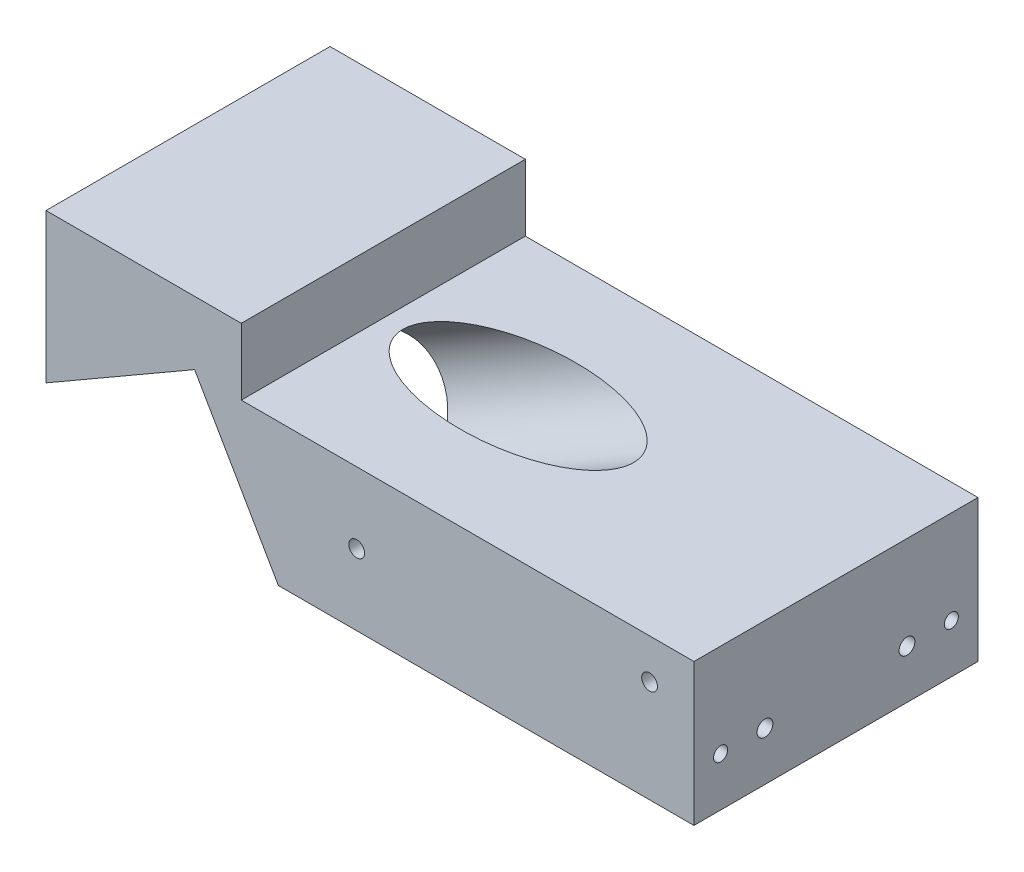
SolidWorks part; units mm, degrees
material "6061-T4 (SS)"
ref_plane "Front Plane" through (0, 0, 0) normal (0, 0, 1) x (1, 0, 0)
ref_plane "Top Plane" through (0, 0, 0) normal (0, 1, 0) x (1, 0, 0)
ref_plane "Right Plane" through (0, 0, 0) normal (1, 0, 0) x (0, 0, -1)
sketch "Sketch1" plane through (0, 0, 0) normal (0, 1, 0) x (1, 0, 0)
  line L1 (-36.5, 16) -> (36.5, 16)
  line L2 (-36.5, 16) -> (-36.5, -16)
  line L3 (-36.5, -16) -> (36.5, -16)
  line L4 (36.5, 16) -> (36.5, -16)
  line L5 (-36.5, 16) -> (36.5, -16) construction
  line L6 (-36.5, -16) -> (36.5, 16) construction
  point P0 (0, 0)
  dimension "D1" = 73
  dimension "D2" = 32
extrude "Boss-Extrude1" add sketch "Sketch1" along normal blind 16
sketch "Sketch78" plane through (0, 0, 16) normal (0, 0, 1) x (1, 0, 0)
  line L1 (-36.5, 16) -> (-14.5, 16)
  line L2 (-36.5, 16) -> (-36.5, 23.5)
  line L3 (-36.5, 23.5) -> (-14.5, 23.5)
  line L4 (-14.5, 16) -> (-14.5, 23.5)
  dimension "D1" = 7.5
  dimension "D2" = 22
extrude "Boss-Extrude4" add sketch "Sketch78" against normal up to surface (32 mm away) up to face at (0, 8, -16)
sketch "Sketch79" plane through (0, 0, -16) normal (0, 0, -1) x (-1, 0, 0)
  line L0 (-32.5, 1.97) -> (23.61, 1.97) construction
  line L1 (-32.5, 1.97) -> (-32.5, 29.2) construction
  line L2 (23.61, 1.97) -> (-20.8992, 27.6674) construction
  line L3 (33.135, 1.97) -> (34.135, 1.97) construction
  line L4 (14.4951, 7.2325) -> (19.7576, 16.3474)
  line L5 (19.7576, 16.3474) -> (36.5, 6.6812)
  line L6 (36.5, 23.5) -> (36.5, 0) construction
  line L7 (14.4951, 7.2325) -> (10.3194, 0)
  line L8 (-36.5, 0) -> (36.5, 0) construction
  line L9 (10.3194, 0) -> (36.5, 0)
  line L10 (36.5, 0) -> (36.5, 6.6812)
  circle A0 centre (23.61, 1.97) radius 9.525 construction
  circle A1 centre (23.61, 1.97) radius 10.525 construction
  dimension "D4" = 19.05
  dimension "D1" = 27.23
  dimension "D2" = 56.11
  dimension "D3" = 30
  dimension "D5" = 1
extrude "Cut-Extrude23" cut sketch "Sketch79" against normal blind 41
sketch "Sketch26" plane through (0, 0, 0) normal (0, -1, 0) x (1, 0, 0)
  line L0 (-10.3194, 16) -> (36.5, 16) construction
  line L1 (36.5, -16) -> (42.85, -16)
  line L2 (36.5, -16) -> (36.5, 16)
  line L3 (36.5, 16) -> (42.85, 16)
  line L4 (42.85, -16) -> (42.85, 16)
  dimension "D1" = 6.35
sketch "Sketch15" plane through (-36.5, 0, 0) normal (-1, 0, 0) x (0, 0, 1)
  line L0 (-10, 14.6812) -> (10, 14.6812) construction
  line L1 (-10, 14.6812) -> (-16, 14.6812) construction
  line L3 (10, 14.6812) -> (16, 14.6812) construction
  line L6 (16, 23.5) -> (16, 6.6812) construction
  line L7 (-16, 23.5) -> (-16, 6.6812) construction
  line L9 (16, 6.6812) -> (-16, 6.6812) construction
  dimension "D3" = 20
  dimension "D4" = 8
sketch "Sketch14" plane through (-13.4261, 5.3809, -20) normal (-0.866, -0.5, 0) x (0, 0, 1)
  line L0 (4, 2.138) -> (20, 2.138) construction
  line L1 (20, 2.138) -> (36, 2.138) construction
  line L2 (36, 12.663) -> (36, -6.2133) construction
  line L3 (4, 12.663) -> (4, -6.2133) construction
  circle A0 centre (20, 2.138) radius 6.5
  dimension "D1" = 13
extrude "Cut-Extrude2" cut sketch "Sketch14" against normal blind 33 and the other way blind 41
hole_wizard "#2-56 Tapped Hole1" positions "Sketch80" profile "Sketch81" tap size "#2-56" standard "ANSI Inch"
sketch "Sketch80" plane through (-36.5, 0, 0) normal (-1, 0, 0) x (0, 0, 1)
  point P0 (-10, 14.6812)
  point P3 (10, 14.6812)
sketch "Sketch81" plane through (-36.5, 14.6812, -10) normal (0, 1, 0) x (0, 0, 1)
  line L0 (0, 0) -> (0, 6.8842)
  line L1 (0, 6.8842) -> (0.889, 6.35)
  line L2 (0.889, 6.35) -> (0.889, 0)
  line L5 (0.889, 0) -> (0, 0)
  line L10 (0, 6.8842) -> (-0.889, 6.35) construction
  line L11 (0, -6.35) -> (0, 107.95) construction
  dimension "Tap Drill Dia." = 1.778
  dimension "Tap Drill Depth" = 6.35
  dimension "Drill Angle" = 118
cosmetic thread "Hole Thread1" parameters "D1"=4.4, "D2"=2.1844
cosmetic thread "Hole Thread2" parameters "D1"=4.4, "D2"=2.1844
sketch "Sketch59" plane through (0, 0, -16) normal (0, 0, -1) x (-1, 0, 0)
  line L0 (36.5, 16) -> (36.5, 0) construction
  line L1 (36.5, 0) -> (-36.5, 0) construction
  line L2 (-36.5, 0) -> (-36.5, 16) construction
  line L3 (36.5, 23.5) -> (36.5, 6.6812) construction
  line L4 (-36.5, 16) -> (36.5, 16) construction
  line L5 (-36.5, 8) -> (36.5, 8) construction
  line L7 (-36.5, 16) -> (14.5, 16) construction
  line L8 (-31.5, 11.5) -> (-31.5, 8) construction
  line L10 (-36.5, 16) -> (-36.5, 0) construction
  point P10 (-31.5, 11.5)
  point P11 (1.5, 8)
  dimension "D1" = 5
  dimension "D2" = 35
  dimension "D3" = 3.5
hole_wizard "#2-56 Tapped Hole2" positions "Sketch82" profile "Sketch83" tap size "#2-56" standard "ANSI Inch"
sketch "Sketch82" plane through (0, 0, -16) normal (0, 0, -1) x (-1, 0, 0)
  point P0 (-31.5, 11.5)
  point P3 (1.5, 8)
sketch "Sketch83" plane through (31.5, 11.5, -16) normal (1, 0, 0) x (0, 1, 0)
  line L0 (0, 0) -> (0, 6.8842)
  line L1 (0, 6.8842) -> (0.889, 6.35)
  line L2 (0.889, 6.35) -> (0.889, 0)
  line L5 (0.889, 0) -> (0, 0)
  line L10 (0, 6.8842) -> (-0.889, 6.35) construction
  line L11 (0, -6.35) -> (0, 107.95) construction
  dimension "Tap Drill Dia." = 1.778
  dimension "Tap Drill Depth" = 6.35
  dimension "Drill Angle" = 118
cosmetic thread "Hole Thread3" parameters "D1"=4.4, "D2"=2.1844
cosmetic thread "Hole Thread4" parameters "D1"=4.4, "D2"=2.1844
hole_wizard "#2-56 Tapped Hole3" positions "Sketch84" profile "Sketch85" tap size "#2-56" standard "ANSI Inch"
sketch "Sketch84" plane through (0, 0, 16) normal (0, 0, 1) x (1, 0, 0)
  point P0 (-1.5, 8)
  point P3 (31.5, 11.5)
sketch "Sketch85" plane through (-1.5, 8, 16) normal (1, 0, 0) x (0, -1, 0)
  line L0 (0, 0) -> (0, 6.8842)
  line L1 (0, 6.8842) -> (0.889, 6.35)
  line L2 (0.889, 6.35) -> (0.889, 0)
  line L5 (0.889, 0) -> (0, 0)
  line L10 (0, 6.8842) -> (-0.889, 6.35) construction
  line L11 (0, -6.35) -> (0, 107.95) construction
  dimension "Tap Drill Dia." = 1.778
  dimension "Tap Drill Depth" = 6.35
  dimension "Drill Angle" = 118
cosmetic thread "Hole Thread5" parameters "D1"=4.4, "D2"=2.1844
cosmetic thread "Hole Thread6" parameters "D1"=4.4, "D2"=2.1844
hole_wizard "#2-56 Tapped Hole4" positions "Sketch86" profile "Sketch87" tap size "#2-56" standard "ANSI Inch"
sketch "Sketch86" plane through (-7.7395, -4.4684, 0) normal (-0.866, -0.5, 0) x (0, 0, 1)
  line L0 (-10, 13.5111) -> (10, 13.5111) construction
  circle A1 centre (0, 13.5111) radius 6.5
  circle A2 centre (0, 13.5111) radius 6.5 construction
  point P0 (-10, 13.5111)
  point P2 (10, 13.5111)
  point P19 (0, 13.5111)
  dimension "D1" = 10
sketch "Sketch87" plane through (-14.4951, 7.2325, -10) normal (0, 0, 1) x (0.5, -0.866, 0)
  line L0 (0, 0) -> (0, 6.8842)
  line L1 (0, 6.8842) -> (0.889, 6.35)
  line L2 (0.889, 6.35) -> (0.889, 0)
  line L5 (0.889, 0) -> (0, 0)
  line L10 (0, 6.8842) -> (-0.889, 6.35) construction
  line L11 (0, -6.35) -> (0, 107.95) construction
  dimension "Tap Drill Dia." = 1.778
  dimension "Tap Drill Depth" = 6.35
  dimension "Drill Angle" = 118
cosmetic thread "Hole Thread7" parameters "D1"=4.4, "D2"=2.1844
cosmetic thread "Hole Thread8" parameters "D1"=4.4, "D2"=2.1844
hole_wizard "#2-56 Tapped Hole5" positions "Sketch89" profile "Sketch90" tap size "#2-56" standard "ANSI Inch"
sketch "Sketch89" plane through (0, 0, -16) normal (0, 0, -1) x (-1, 0, 0)
  line L0 (36.5, 19) -> (31.5, 19) construction
  line L1 (36.5, 23.5) -> (36.5, 6.6812) construction
  line L2 (31.5, 19) -> (31.5, 23.5) construction
  line L3 (36.5, 23.5) -> (14.5, 23.5) construction
  point P0 (31.5, 19)
  dimension "D1" = 4.5
  dimension "D2" = 5
sketch "Sketch90" plane through (-31.5, 19, -16) normal (1, 0, 0) x (0, 1, 0)
  line L0 (0, 0) -> (0, 5.2942)
  line L1 (0, 5.2942) -> (0.889, 4.76)
  line L2 (0.889, 4.76) -> (0.889, 0)
  line L5 (0.889, 0) -> (0, 0)
  line L10 (0, 5.2942) -> (-0.889, 4.76) construction
  line L11 (0, -6.35) -> (0, 107.95) construction
  dimension "Tap Drill Dia." = 1.778
  dimension "Tap Drill Depth" = 4.76
  dimension "Drill Angle" = 118
cosmetic thread "Hole Thread9" parameters "D1"=4.37, "D2"=2.1844
hole_wizard "#2-56 Tapped Hole7" positions "Sketch103" profile "Sketch104" tap size "#2-56" standard "ANSI Inch"
sketch "Sketch103" plane through (36.5, 0, 0) normal (1, 0, 0) x (0, 0, -1)
  line L0 (-16, 5.5) -> (-8, 5.5) construction
  line L1 (-16, 16) -> (-16, 0) construction
  line L2 (-8, 5.5) -> (8, 5.5) construction
  line L3 (8, 5.5) -> (16, 5.5) construction
  line L4 (16, 16) -> (16, 0) construction
  line L5 (16, 5.5) -> (16, 8) construction
  point P0 (-8, 5.5)
  point P3 (8, 5.5)
  dimension "D1" = 2.5
  dimension "D2" = 8
sketch "Sketch104" plane through (36.5, 5.5, 8) normal (0, 1, 0) x (0, 0, -1)
  line L0 (0, 0) -> (0, 15.5342)
  line L1 (0, 15.5342) -> (0.889, 15)
  line L2 (0.889, 15) -> (0.889, 0)
  line L5 (0.889, 0) -> (0, 0)
  line L10 (0, 15.5342) -> (-0.889, 15) construction
  line L11 (0, -6.35) -> (0, 107.95) construction
  dimension "Tap Drill Dia." = 1.778
  dimension "Tap Drill Depth" = 15
  dimension "Drill Angle" = 118
cosmetic thread "Hole Thread10" parameters "D1"=4.37, "D2"=2.1844
cosmetic thread "Hole Thread11" parameters "D1"=4.37, "D2"=2.1844
hole_wizard "1/16 (0.0625) Dowel Hole1" positions "Sketch105" profile "Sketch106" hole size "1/16" standard "ANSI Inch"
sketch "Sketch105" plane through (36.5, 0, 0) normal (1, 0, 0) x (0, 0, -1)
  line L0 (-13, 5.5) -> (-8, 5.5) construction
  line L1 (-8, 5.5) -> (8, 5.5) construction
  line L2 (8, 5.5) -> (13, 5.5) construction
  line L7 (-16, 16) -> (-16, 0) construction
  point P0 (13, 5.5)
  point P2 (-13, 5.5)
  dimension "D1" = 3
sketch "Sketch106" plane through (36.5, 5.5, -13) normal (0, 1, 0) x (0, 0, -1)
  line L0 (0, 0) -> (0, 6.9769)
  line L1 (0, 6.9769) -> (0.7937, 6.5)
  line L2 (0.7937, 6.5) -> (0.7937, 0)
  line L5 (0.7937, 0) -> (0, 0)
  line L10 (0, 6.9769) -> (-0.7938, 6.5) construction
  line L11 (0, -6.35) -> (0, 107.95) construction
  dimension "Hole Dia." = 1.5875
  dimension "Hole Depth" = 6.5
  dimension "Drill Angle" = 118
